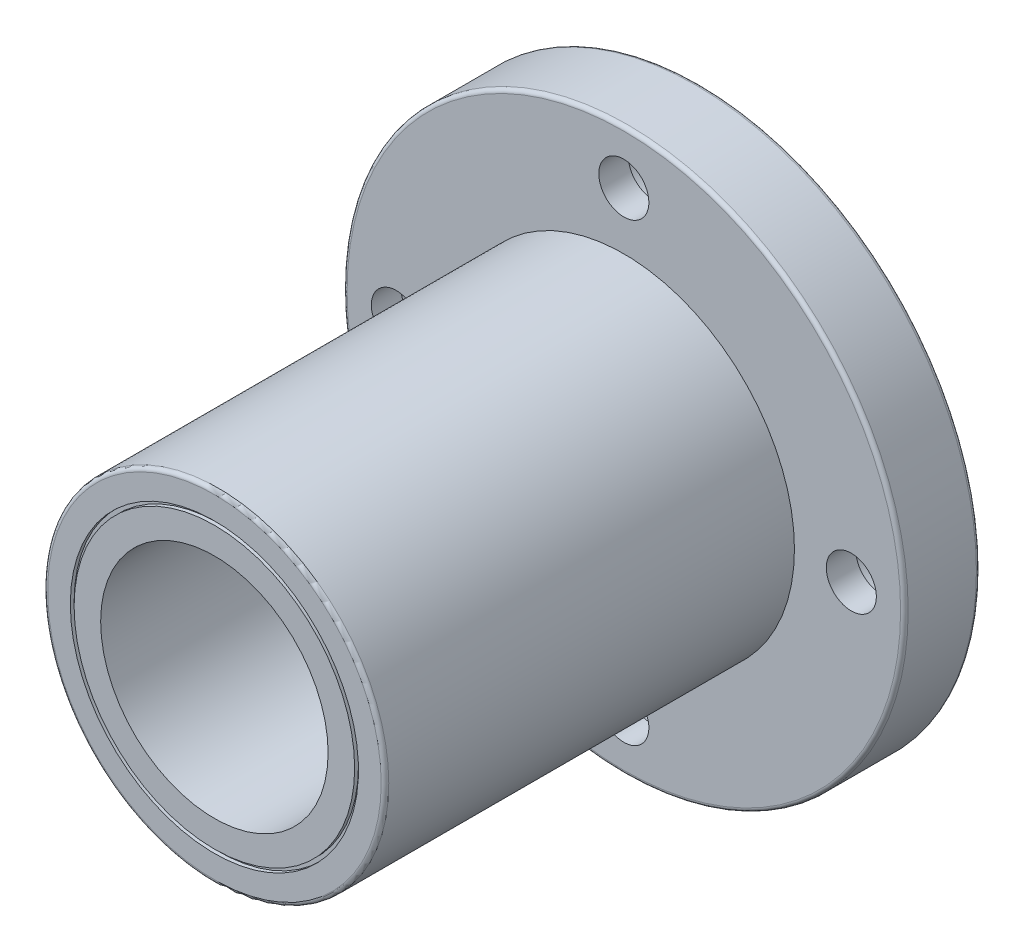
SolidWorks part; units mm, degrees
material "AISI 316 Отожженная нержавеющая сталь. полоса (SS)"
ref_plane "Plano frontal" through (0, 0, 0) normal (0, 0, 1) x (1, 0, 0)
ref_plane "Plano superior" through (0, 0, 0) normal (0, 1, 0) x (1, 0, 0)
ref_plane "Plano direito" through (0, 0, 0) normal (1, 0, 0) x (0, 0, -1)
sketch "Esboço1" plane through (0, 0, 0) normal (1, 0, 0) x (0, 0, -1)
  line L0 (0, 15) -> (0, 18.5)
  line L1 (0, 37) -> (-10, 37)
  line L2 (-10, 37) -> (-10, 22.5)
  line L3 (-10, 22.5) -> (-64, 22.5)
  line L4 (-64, 22.5) -> (-64, 19)
  line L5 (-64, 15) -> (0, 15)
  line L6 (0, 0) -> (-226.2321, 0) construction
  line L7 (-64, 19) -> (-63.5, 19)
  line L8 (-63.5, 19) -> (-63.5, 18.5)
  line L9 (-63.5, 18.5) -> (-64, 18.5)
  line L10 (0, 22.5) -> (-0.5, 22.5)
  line L11 (-0.5, 22.5) -> (-0.5, 22)
  line L12 (-0.5, 22) -> (0, 22)
  line L13 (0, 22.5) -> (0, 37)
  line L14 (-64, 18.5) -> (-64, 15)
  line L15 (0, 19) -> (-0.5, 19)
  line L16 (-0.5, 19) -> (-0.5, 18.5)
  line L17 (-0.5, 18.5) -> (0, 18.5)
  line L18 (0, 19) -> (0, 22)
  dimension "D1" = 64
  dimension "D2" = 45
  dimension "D3" = 30
  dimension "D4" = 74
  dimension "D5" = 10
  dimension "D6" = 0.5
  dimension "D7" = 0.5
  dimension "D8" = 0.5
  dimension "D9" = 0.5
  dimension "D10" = 0.5
  dimension "D11" = 0.5
revolve "Revolução1" add sketch "Esboço1" angle 360 about L6
sketch "Esboço5" plane through (0, 0, 0) normal (1, 0, 0) x (0, 0, -1)
  line L0 (0, 35.5) -> (-6.1, 35.5)
  line L1 (0, -37) -> (0, 37) construction
  line L2 (-6.1, 35.5) -> (-6.1, 33.3)
  line L3 (-6.1, 33.3) -> (-10, 33.3)
  line L4 (-10, 37) -> (-10, -37) construction
  line L5 (-10, 33.3) -> (-10, 30)
  line L6 (-10, 30) -> (0, 30)
  line L7 (0, 30) -> (0, 35.5)
  line L8 (0, 30) -> (2.2336, 30) construction
  line L9 (0, 0) -> (9.7959, 0) construction
  dimension "D1" = 11
  dimension "D2" = 6.6
  dimension "D3" = 6.1
  dimension "D4" = 60
revolve "Corte-Revolução1" cut sketch "Esboço5" angle 360 about L8
pattern_circular "PadrãoCircular1" count 4 over 360 about axis through (0, 0, 0) along (0, 0, 1) of "Corte-Revolução1"
fillet "Filete1" radius 0.5 3 edges at (-37, 0, 0) (-37, 0, 10) (-22.5, 0, 64)
